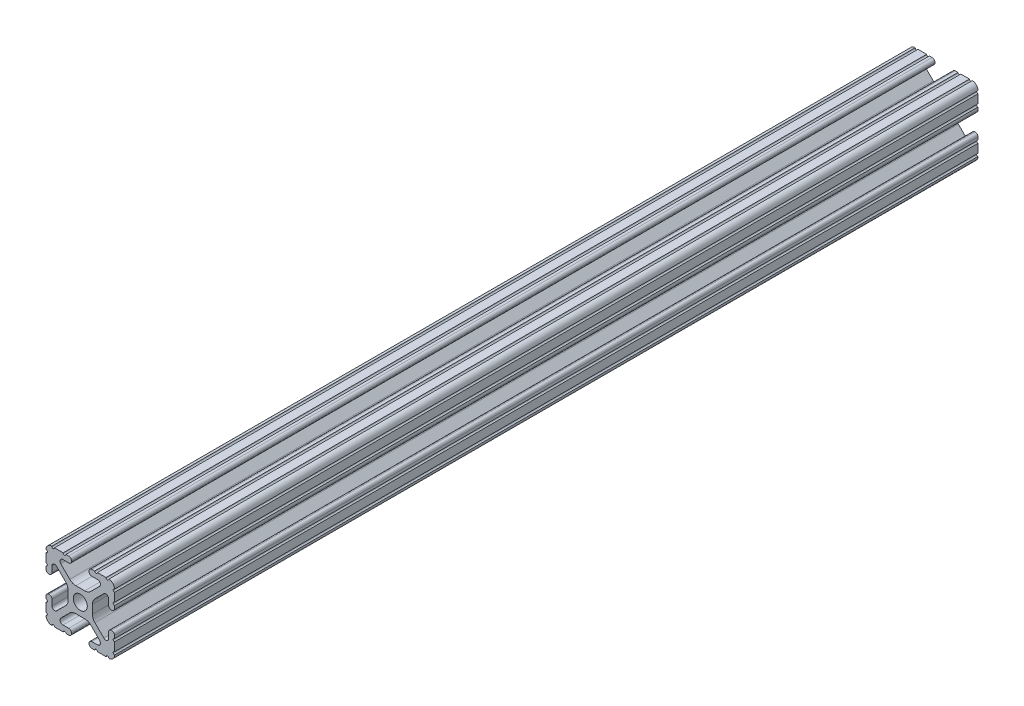
SolidWorks part; units mm, degrees
material "6105-T5 Aluminum"
ref_plane "Front Plane" through (0, 0, 0) normal (0, 0, 1) x (1, 0, 0)
ref_plane "Top Plane" through (0, 0, 0) normal (0, 1, 0) x (1, 0, 0)
ref_plane "Right Plane" through (0, 0, 0) normal (1, 0, 0) x (0, 0, -1)
sketch "Sketch1" plane through (0, 0, 0) normal (0, 0, 1) x (1, 0, 0)
  line L0 (-7.207, 8.7244) -> (-3.8983, 5.4232)
  line L1 (-4.2875, 10.4902) -> (-6.4768, 10.4902)
  line L2 (-3.2385, 11.651) -> (-3.2385, 11.5392)
  line L3 (-5.3171, 12.7) -> (-4.2875, 12.7)
  line L4 (0, 13.4005) -> (0, -14.8534) construction
  line L5 (12.7, 0) -> (-13.9989, 0) construction
  line L6 (-9.5504, 12.7) -> (-6.3331, 12.7)
  line L7 (-12.7, 6.3331) -> (-12.7, 9.5504)
  line L8 (-12.7, 4.2875) -> (-12.7, 5.3171)
  line L9 (-11.5392, 3.2385) -> (-11.651, 3.2385)
  line L10 (-10.4902, 6.4021) -> (-10.4902, 4.2875)
  line L11 (-5.441, 3.8408) -> (-8.7371, 7.1294)
  line L12 (-4.5085, -1.5932) -> (-4.5085, 1.5932)
  line L13 (-1.7093, -4.4958) -> (1.7093, -4.4958)
  line L14 (3.9523, -5.4237) -> (7.1797, -8.6452)
  line L15 (6.4164, -10.4902) -> (4.2875, -10.4902)
  line L16 (3.2385, -11.5392) -> (3.2385, -11.651)
  line L17 (4.2875, -12.7) -> (5.3171, -12.7)
  line L18 (6.3331, -12.7) -> (9.5504, -12.7)
  line L19 (12.7, -9.5504) -> (12.7, -6.3331)
  line L20 (12.7, -5.3171) -> (12.7, -4.2875)
  line L21 (11.651, -3.2385) -> (11.5392, -3.2385)
  line L22 (10.4902, -4.2875) -> (10.4902, -6.4021)
  line L23 (8.7371, -7.1294) -> (5.441, -3.8408)
  line L24 (4.5085, -1.5932) -> (4.5085, 1.5932)
  line L25 (5.441, 3.8408) -> (8.7371, 7.1294)
  line L26 (10.4902, 6.4021) -> (10.4902, 4.2875)
  line L27 (11.5392, 3.2385) -> (11.651, 3.2385)
  line L28 (12.7, 4.2875) -> (12.7, 5.3171)
  line L29 (12.7, 6.3331) -> (12.7, 9.5504)
  line L30 (9.5504, 12.7) -> (6.3331, 12.7)
  line L31 (5.3171, 12.7) -> (4.2875, 12.7)
  line L32 (3.2385, 11.651) -> (3.2385, 11.5392)
  line L33 (4.2875, 10.4902) -> (6.4768, 10.4902)
  line L34 (7.207, 8.7244) -> (3.8983, 5.4232)
  line L35 (1.6558, 4.4958) -> (-1.6558, 4.4958)
  line L36 (-8.7371, -7.1294) -> (-5.441, -3.8408)
  line L37 (-10.4902, -4.2875) -> (-10.4902, -6.4021)
  line L38 (-11.651, -3.2385) -> (-11.5392, -3.2385)
  line L39 (-12.7, -5.3171) -> (-12.7, -4.2875)
  line L40 (-12.7, -9.5504) -> (-12.7, -6.3331)
  line L41 (-6.3331, -12.7) -> (-9.5504, -12.7)
  line L42 (-4.2875, -12.7) -> (-5.3171, -12.7)
  line L43 (-3.2385, -11.5392) -> (-3.2385, -11.651)
  line L44 (-6.4164, -10.4902) -> (-4.2875, -10.4902)
  line L45 (-3.9523, -5.4237) -> (-7.1797, -8.6452)
  arc A0 (-7.207, 8.7244) -> (-6.4768, 10.4902) centre (-6.4768, 9.4563) cw
  arc A1 (-3.2385, 11.5392) -> (-4.2875, 10.4902) centre (-4.2875, 11.5392) cw
  arc A2 (-4.2875, 12.7) -> (-3.2385, 11.651) centre (-4.2875, 11.651) cw
  arc A3 (-5.3171, 12.7) -> (-6.3331, 12.7) centre (-5.8251, 12.7) cw
  arc A4 (-9.5504, 12.7) -> (-10.5664, 12.6998) centre (-10.0584, 12.7) cw
  arc A5 (-12.6998, 10.5664) -> (-10.5664, 12.6998) centre (-10.5918, 10.5918) cw
  arc A6 (-12.6998, 10.5664) -> (-12.7, 9.5504) centre (-12.7, 10.0584) cw
  arc A7 (-12.7, 6.3331) -> (-12.7, 5.3171) centre (-12.7, 5.8251) cw
  arc A8 (-11.651, 3.2385) -> (-12.7, 4.2875) centre (-11.651, 4.2875) cw
  arc A9 (-10.4902, 4.2875) -> (-11.5392, 3.2385) centre (-11.5392, 4.2875) cw
  circle A10 centre (0, 0) radius 2.6035
  arc A11 (-10.4902, 6.4021) -> (-8.7371, 7.1294) centre (-9.4628, 6.4021) cw
  arc A12 (-5.441, 3.8408) -> (-4.5085, 1.5932) centre (-7.6835, 1.5932) cw
  arc A13 (-4.5085, -1.5932) -> (-5.441, -3.8408) centre (-7.6835, -1.5932) cw
  arc A14 (-8.7371, -7.1294) -> (-10.4902, -6.4021) centre (-9.4628, -6.4021) cw
  arc A15 (-1.7093, -4.4958) -> (-3.9523, -5.4237) centre (-1.7093, -7.6708) ccw
  arc A16 (3.9523, -5.4237) -> (1.7093, -4.4958) centre (1.7093, -7.6708) ccw
  arc A17 (6.4164, -10.4902) -> (7.1797, -8.6452) centre (6.4164, -9.4098) ccw
  arc A18 (4.2875, -10.4902) -> (3.2385, -11.5392) centre (4.2875, -11.5392) ccw
  arc A19 (3.2385, -11.651) -> (4.2875, -12.7) centre (4.2875, -11.651) ccw
  arc A20 (6.3331, -12.7) -> (5.3171, -12.7) centre (5.8251, -12.7) ccw
  arc A21 (10.5664, -12.6998) -> (9.5504, -12.7) centre (10.0584, -12.7) ccw
  arc A22 (10.5664, -12.6998) -> (12.6998, -10.5664) centre (10.5918, -10.5918) ccw
  arc A23 (12.7, -9.5504) -> (12.6998, -10.5664) centre (12.7, -10.0584) ccw
  arc A24 (12.7, -5.3171) -> (12.7, -6.3331) centre (12.7, -5.8251) ccw
  arc A25 (12.7, -4.2875) -> (11.651, -3.2385) centre (11.651, -4.2875) ccw
  arc A26 (11.5392, -3.2385) -> (10.4902, -4.2875) centre (11.5392, -4.2875) ccw
  arc A27 (8.7371, -7.1294) -> (10.4902, -6.4021) centre (9.4628, -6.4021) ccw
  arc A28 (4.5085, -1.5932) -> (5.441, -3.8408) centre (7.6835, -1.5932) ccw
  arc A29 (5.441, 3.8408) -> (4.5085, 1.5932) centre (7.6835, 1.5932) ccw
  arc A30 (10.4902, 6.4021) -> (8.7371, 7.1294) centre (9.4628, 6.4021) ccw
  arc A31 (10.4902, 4.2875) -> (11.5392, 3.2385) centre (11.5392, 4.2875) ccw
  arc A32 (11.651, 3.2385) -> (12.7, 4.2875) centre (11.651, 4.2875) ccw
  arc A33 (12.7, 6.3331) -> (12.7, 5.3171) centre (12.7, 5.8251) ccw
  arc A34 (12.6998, 10.5664) -> (12.7, 9.5504) centre (12.7, 10.0584) ccw
  arc A35 (12.6998, 10.5664) -> (10.5664, 12.6998) centre (10.5918, 10.5918) ccw
  arc A36 (9.5504, 12.7) -> (10.5664, 12.6998) centre (10.0584, 12.7) ccw
  arc A37 (5.3171, 12.7) -> (6.3331, 12.7) centre (5.8251, 12.7) ccw
  arc A38 (4.2875, 12.7) -> (3.2385, 11.651) centre (4.2875, 11.651) ccw
  arc A39 (3.2385, 11.5392) -> (4.2875, 10.4902) centre (4.2875, 11.5392) ccw
  arc A40 (7.207, 8.7244) -> (6.4768, 10.4902) centre (6.4768, 9.4563) ccw
  arc A41 (1.6558, 4.4958) -> (3.8983, 5.4232) centre (1.6558, 7.6708) ccw
  arc A42 (-1.6558, 4.4958) -> (-3.8983, 5.4232) centre (-1.6558, 7.6708) cw
  arc A43 (-11.5392, -3.2385) -> (-10.4902, -4.2875) centre (-11.5392, -4.2875) cw
  arc A44 (-12.7, -4.2875) -> (-11.651, -3.2385) centre (-11.651, -4.2875) cw
  arc A45 (-12.7, -5.3171) -> (-12.7, -6.3331) centre (-12.7, -5.8251) cw
  arc A46 (-12.7, -9.5504) -> (-12.6998, -10.5664) centre (-12.7, -10.0584) cw
  arc A47 (-10.5664, -12.6998) -> (-12.6998, -10.5664) centre (-10.5918, -10.5918) cw
  arc A48 (-10.5664, -12.6998) -> (-9.5504, -12.7) centre (-10.0584, -12.7) cw
  arc A49 (-6.3331, -12.7) -> (-5.3171, -12.7) centre (-5.8251, -12.7) cw
  arc A50 (-3.2385, -11.651) -> (-4.2875, -12.7) centre (-4.2875, -11.651) cw
  arc A51 (-4.2875, -10.4902) -> (-3.2385, -11.5392) centre (-4.2875, -11.5392) cw
  arc A52 (-6.4164, -10.4902) -> (-7.1797, -8.6452) centre (-6.4164, -9.4098) cw
  dimension "D1" = 5.207
  dimension "D9" = 14.859
  dimension "D2" = 25.4
  dimension "D3" = 12.7
  dimension "D4" = 6.477
  dimension "D5" = 8.2042
  dimension "D6" = 9.017
  dimension "D8" = 2.2098
  dimension "D10" = 2.2098
extrude "Extrude1" add sketch "Sketch1" against normal mid plane 320
